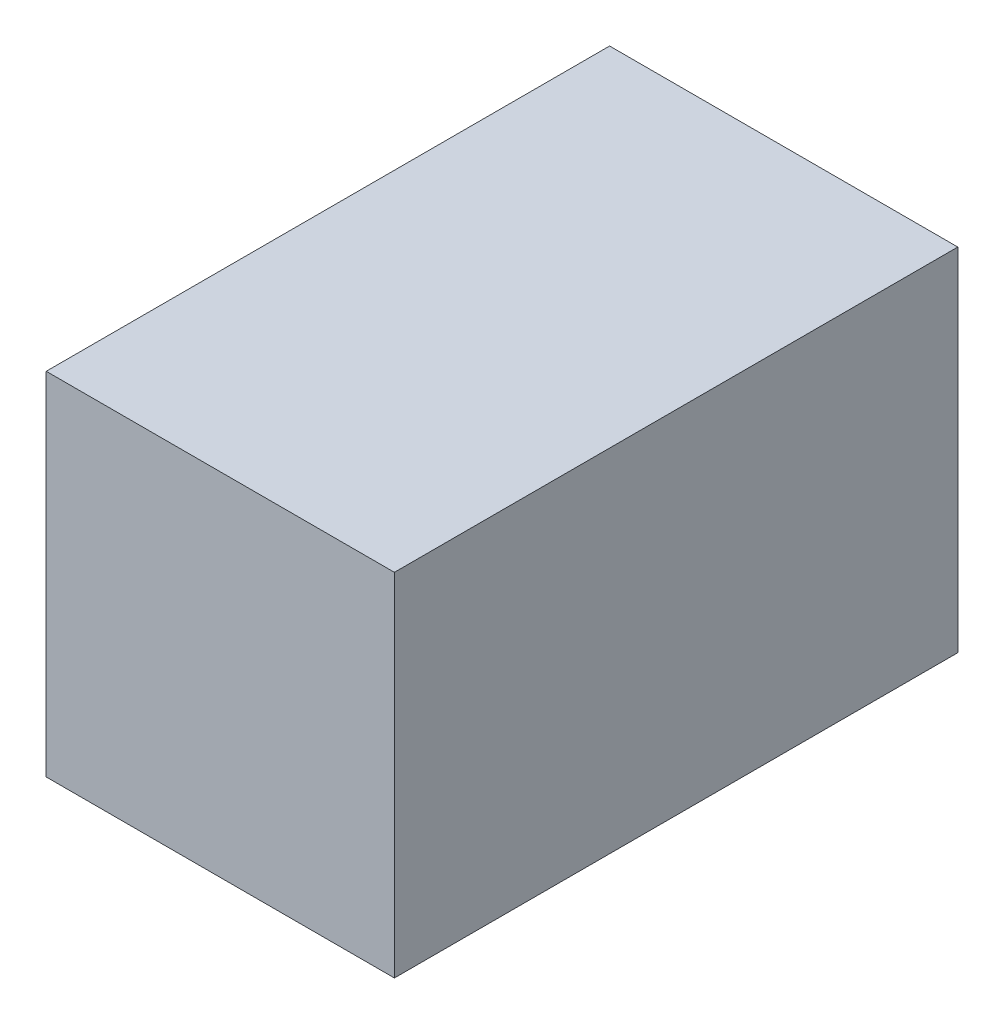
SolidWorks part; units mm, degrees
ref_plane "Front Plane" through (0, 0, 0) normal (0, 0, 1) x (1, 0, 0)
ref_plane "Top Plane" through (0, 0, 0) normal (0, 1, 0) x (1, 0, 0)
ref_plane "Right Plane" through (0, 0, 0) normal (1, 0, 0) x (0, 0, -1)
sketch "Sketch1" plane through (0, 0, 0) normal (0, 1, 0) x (1, 0, 0)
  line L1 (0, 0) -> (49.1109, 0)
  line L2 (0, 0) -> (0, 79.4639)
  line L3 (0, 79.4639) -> (49.1109, 79.4639)
  line L4 (49.1109, 0) -> (49.1109, 79.4639)
  dimension "D1" = 79.4639
  dimension "D2" = 49.1109
extrude "Boss-Extrude1" add sketch "Sketch1" along normal blind 49.5554
